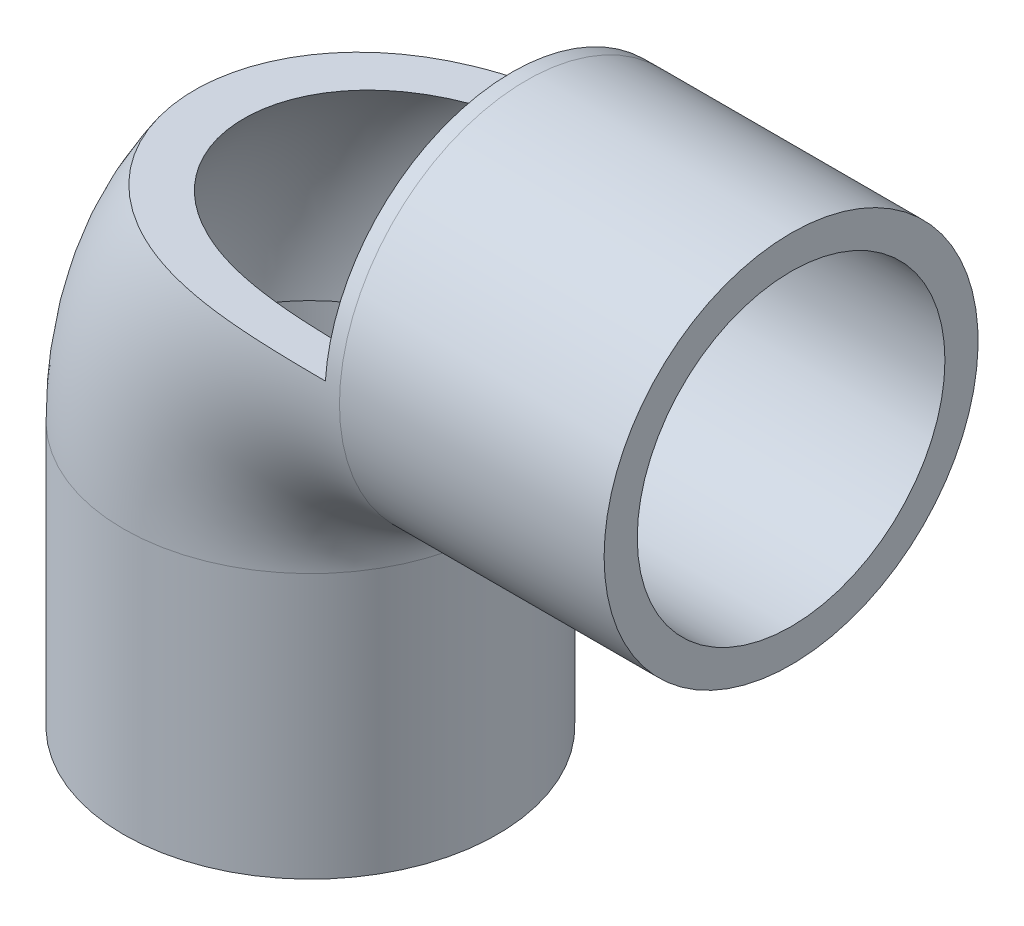
SolidWorks part; units mm, degrees
ref_plane "Front Plane" through (0, 0, 0) normal (0, 0, 1) x (1, 0, 0)
ref_plane "Top Plane" through (0, 0, 0) normal (0, 1, 0) x (1, 0, 0)
ref_plane "Right Plane" through (0, 0, 0) normal (1, 0, 0) x (0, 0, -1)
sketch "Sketch1" plane through (0, 0, 0) normal (0, 1, 0) x (1, 0, 0)
  circle A0 centre (0, 0) radius 16.7957
  circle A2 centre (0, 0) radius 20.4153
  dimension "D1" = 33.5915
  dimension "D2" = 40.8305
extrude "Boss-Extrude1" add sketch "Sketch1" along normal blind 28.8925
sketch "Sketch2" plane through (0, 28.8925, 0) normal (0, 1, 0) x (1, 0, 0)
  line L0 (0, 0) -> (20.4153, 0)
  line L1 (20.4153, 0) -> (23.5903, 0)
  line L2 (23.5903, -20.4153) -> (23.5902, 20.4153)
  circle A0 centre (0, 0) radius 20.4153
  circle A2 centre (0, 0) radius 16.0972
  point P8 (23.5903, 0)
revolve "Revolve1" add sketch "Sketch2" angle 90 about L2
sketch "Sketch3" plane through (23.5902, 0, 0) normal (1, 0, 0) x (0, 0, -1)
  circle A0 centre (0, 52.4828) radius 20.4153
  circle A1 centre (0, 52.4828) radius 16.7958
  dimension "D1" = 33.5915
extrude "Boss-Extrude2" add sketch "Sketch3" along normal blind 28.8925
sketch "Sketch4" plane through (0, 0, 0) normal (0, -1, 0) x (1, 0, 0)
  circle A0 centre (0, 0) radius 20.4153 construction
  point P0 (0, -20.4153)
extrude "Cut-Extrude2" cut sketch "Sketch5" against normal blind 66.9925 contours L6 L5 L4 L3
sketch "Sketch5" plane through (0, 28.8925, -20.4153) normal (0, 0, -1) x (-1, 0, 0)
  line L0 (-52.4828, 44.0055) -> (-52.4828, 24.9555)
  line L1 (-52.4828, 44.0055) -> (-52.4828, 3.175) construction
  line L2 (-52.4828, 24.9555) -> (-22.0028, 24.9555)
  line L3 (-22.0028, 24.9555) -> (-22.0028, 44.0055)
  line L4 (-22.0028, 44.0055) -> (20.4152, 44.0055)
  line L5 (20.4152, 44.0055) -> (20.4152, 24.9555)
  line L6 (20.4152, 24.9555) -> (-22.0028, 24.9555)
  line L7 (20.4152, 24.9555) -> (-22.0028, 24.9555)
  dimension "D1" = 19.05
  dimension "D2" = 30.48
ref_plane "Plane1" through (0, 28.8925, -20.4153) normal (0, 0, -1) x (-1, 0, 0)
